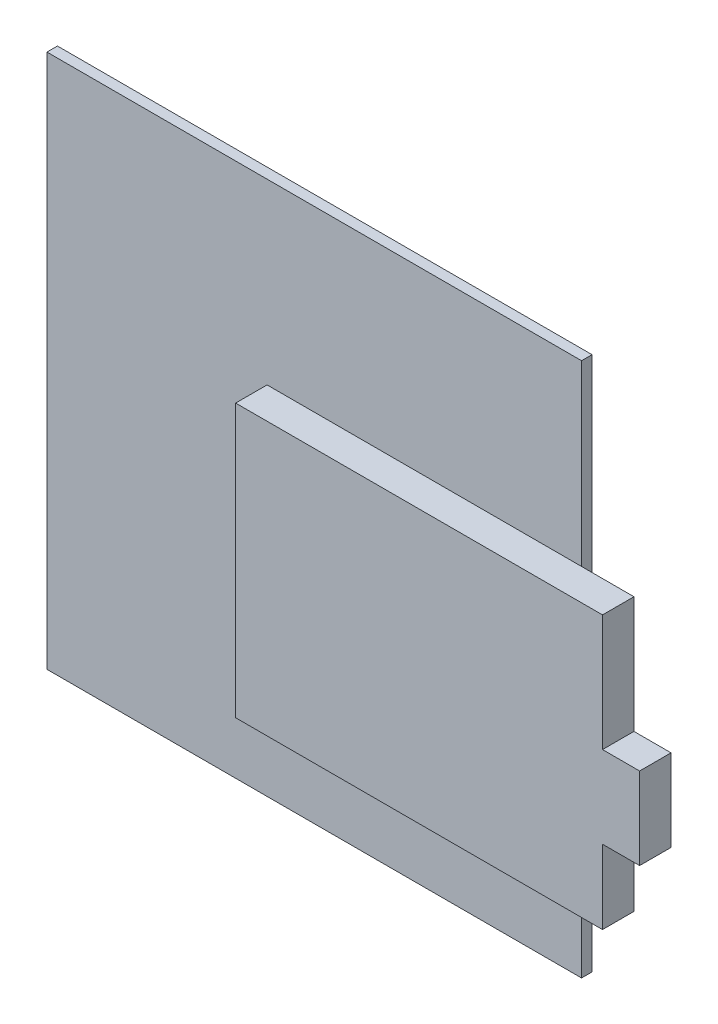
SolidWorks part; units mm, degrees
ref_plane "Alzado" through (0, 0, 0) normal (0, 0, 1) x (1, 0, 0)
ref_plane "Planta" through (0, 0, 0) normal (0, 1, 0) x (1, 0, 0)
ref_plane "Vista lateral" through (0, 0, 0) normal (1, 0, 0) x (0, 0, -1)
sketch "Croquis1" plane through (0, 0, 0) normal (0, 0, 1) x (1, 0, 0)
  line L1 (0, 0) -> (51, 0)
  line L2 (0, 0) -> (0, -52)
  line L3 (0, -52) -> (51, -52)
  line L4 (51, 0) -> (51, -52)
  dimension "D1" = 52
  dimension "D2" = 51
extrude "Saliente-Extruir1" add sketch "Croquis1" along normal blind 1
sketch "Croquis2" plane through (0, 0, 1) normal (0, 0, 1) x (1, 0, 0)
  line L0 (51, -52) -> (51, 0) construction
  line L1 (0, -52) -> (51, -52) construction
  line L2 (21, -18) -> (56, -18)
  line L3 (21, -18) -> (21, -44)
  line L4 (21, -44) -> (56, -44)
  line L5 (56, -18) -> (56, -44)
  line L8 (53.404, -29.1272) -> (59.5381, -29.1272)
  line L9 (53.404, -29.1272) -> (53.404, -36.9451)
  line L10 (53.404, -36.9451) -> (59.5381, -36.9451)
  line L11 (59.5381, -29.1272) -> (59.5381, -36.9451)
  line M7 (51, -52) -> (51, 0)
  dimension "D1" = 35
  dimension "D2" = 26
  dimension "D3" = 8
  dimension "D4" = 5
extrude "Saliente-Extruir2" add sketch "Croquis2" along normal blind 3 contours L3 L4 L2 M7 | L11 L8 L5 L10 | L9 L10 L5 L8 | L10 L9 L8 L5 L2 L4 M7
sketch "Croquis3" plane through (0, 0, 1) normal (0, 0, 1) x (1, 0, 0)
  line L0 (0, -1) -> (51, -1)
  line L1 (0, -52) -> (51, -52)
  line L2 (0, -52) -> (0, 0)
  line L3 (0, 0) -> (51, 0)
  line L4 (51, -52) -> (51, 0)
  line M9 (51, -18) -> (51, 0)
  line M10 (51, 0) -> (0, 0)
  line M11 (0, 0) -> (0, -52)
  dimension "D1" = 51
extrude "Cortar-Extruir2" cut sketch "Croquis3" against normal blind 3 contours L0 M11 M9 M10
